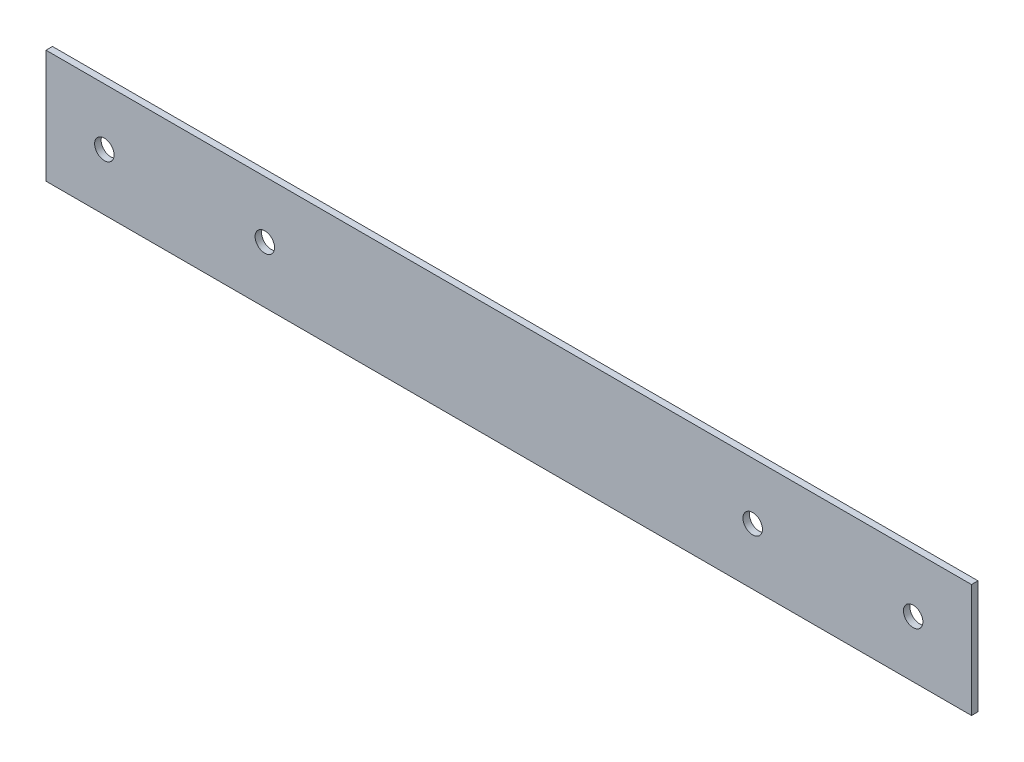
SolidWorks part; units mm, degrees
ref_plane "Front Plane" through (0, 0, 0) normal (0, 0, 1) x (1, 0, 0)
ref_plane "Top Plane" through (0, 0, 0) normal (0, 1, 0) x (1, 0, 0)
ref_plane "Right Plane" through (0, 0, 0) normal (1, 0, 0) x (0, 0, -1)
sketch "Sketch1" plane through (0, 0, 0) normal (0, 0, 1) x (1, 0, 0)
  line L0 (0, 80.5593) -> (0, -41.1981) construction
  line L1 (-142.75, 17.5) -> (142.75, 17.5)
  line L2 (-142.75, 17.5) -> (-142.75, -17.5)
  line L3 (-142.75, -17.5) -> (142.75, -17.5)
  line L4 (142.75, 17.5) -> (142.75, -17.5)
  line L5 (-142.75, 17.5) -> (142.75, -17.5) construction
  line L6 (-142.75, -17.5) -> (142.75, 17.5) construction
  line L7 (-100, 11.3156) -> (-100, -11.0719) construction
  circle A0 centre (-124.75, 0) radius 3
  circle A1 centre (-75.25, 0) radius 3
  circle A2 centre (75.25, 0) radius 3
  circle A3 centre (124.75, 0) radius 3
  point P0 (0, 0)
  dimension "D7" = 6
  dimension "D8" = 6
  dimension "D1" = 285.5
  dimension "D2" = 35
  dimension "D3" = 42.75
  dimension "D4" = 49.5
  dimension "D5" = 24.75
  dimension "D6" = 17.5
  dimension "D9" = 24.75
extrude "Boss-Extrude1" add sketch "Sketch1" along normal blind 2
